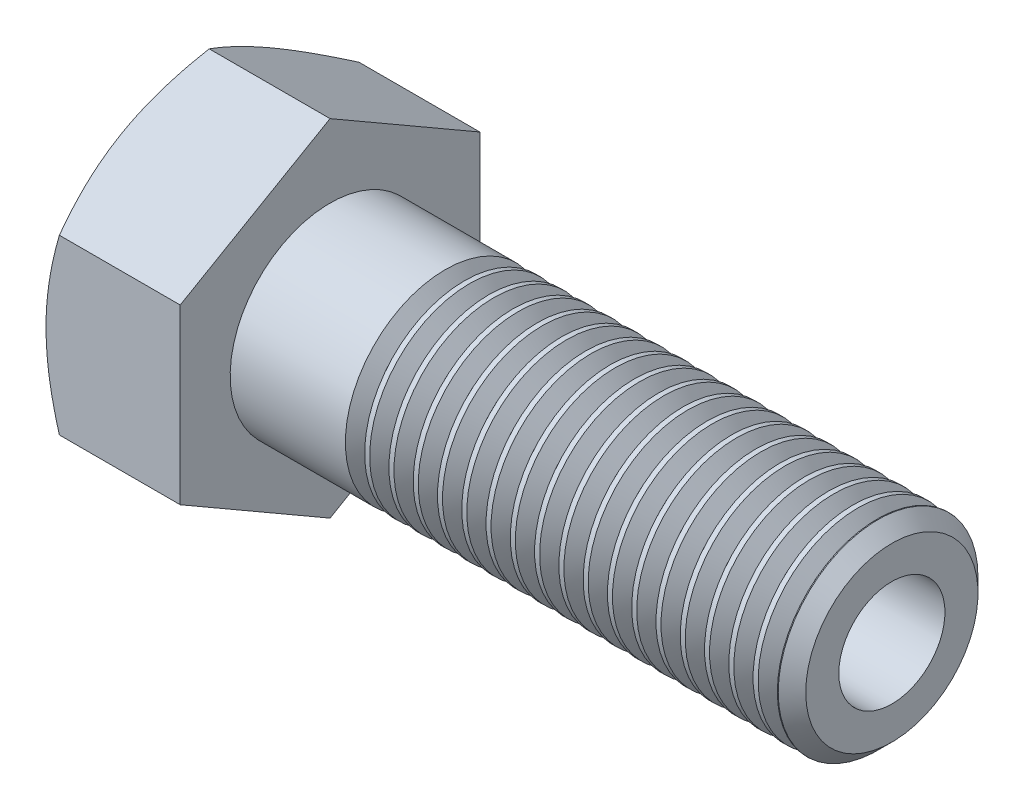
SolidWorks part; units mm, degrees
extrude "BaseHead" add sketch "Sketch1" along normal blind 10.75
sketch "Sketch1" plane through (0, 0, 0) normal (1, 0, 0) x (0, 0, -1)
  line L0 (12, 6.9282) -> (12, -6.9282)
  line L1 (-12, 6.9282) -> (-12, -6.9282)
  line L2 (12, -6.9282) -> (0, -13.8564)
  line L3 (0, -13.8564) -> (-12, -6.9282)
  line L4 (12, 6.9282) -> (0, 13.8564)
  line L5 (0, 13.8564) -> (-12, 6.9282)
  dimension "Width_flats" = 24
  dimension "D2" = 120
  dimension "D3" = 12
  dimension "D4" = 12
  dimension "D5" = 12
ref_plane "Plane1" through (0, 0, 0) normal (0, 0, 1) x (1, 0, 0)
ref_plane "Plane2" through (0, 0, 0) normal (0, 1, 0) x (1, 0, 0)
ref_plane "Plane3" through (0, 0, 0) normal (1, 0, 0) x (0, 0, -1)
sketch "BodySke" plane through (0, 0, 0) normal (0, 0, 1) x (1, 0, 0)
  line L0 (0, 6.9282) -> (0, -6.9282) construction
  line L1 (0, 0) -> (55.75, 0)
  line L2 (0, 0) -> (0, 8)
  line L3 (0, 8) -> (54.6485, 8)
  line L4 (55.75, 0) -> (55.75, 6.8985)
  line L5 (10.75, 13.8564) -> (10.75, 6.9282) construction
  line L6 (55.75, 6.8985) -> (54.6485, 8)
  line L7 (0, 0) -> (96.52, 0) construction
  line L8 (55.75, -6.8985) -> (54.6485, -8) construction
  line L9 (0, -8) -> (54.6485, -8) construction
  line L10 (12.75, 15.24) -> (12.75, -1.27) construction
  line L11 (20.75, 15.24) -> (20.75, -1.27) construction
  line L12 (10.75, 6.9282) -> (10.75, -6.9282) construction
  dimension "Diameter" = 16
revolve "BaseBody" add sketch "BodySke"
cosmetic thread "ThreadCosmetic" [suppressed]
fillet "HeadFillet" [suppressed] radius 0.6
sketch "Sketch3" plane through (0, 0, 0) normal (0, 0, 1) x (1, 0, 0)
  line L0 (0, 12) -> (3.9585, 18.8564)
  line L1 (0, 13.8564) -> (0, 6.9282) construction
  line L2 (3.9585, 18.8564) -> (3.9585, 23.8564)
  line L3 (3.9585, 23.8564) -> (-10, 23.8564)
  line L4 (-10, 23.8564) -> (-10, 12)
  line L5 (-10, 12) -> (0, 12)
  line L6 (0, 0) -> (99.06, 0) construction
  line L7 (10.75, 13.8564) -> (0, 13.8564) construction
  dimension "D1" = 12
  dimension "D2" = 5
  dimension "D3" = 10
  dimension "D4" = 5
  dimension "Head_ch_ang" = 30
revolve "HeadChamfer" cut sketch "Sketch3" angle 360 about L6
sketch "ThdSchSke" plane through (0, 0, 0) normal (0, 0, 1) x (1, 0, 0)
  line L0 (20.75, -6.8985) -> (19.9787, -8)
  line L1 (20.75, -6.8985) -> (21.5213, -8)
  line L2 (21.5213, -8) -> (21.5213, -10)
  line L3 (-3.175, 0) -> (5.1513, 0) construction
  line L5 (21.5213, -10) -> (19.9787, -10)
  line L6 (19.9787, -10) -> (19.9787, -8)
  dimension "Thread_minor" = 13.797
  dimension "Diameter" = 16
  dimension "Start" = 20.75
revolve "ThreadSchematic" cut sketch "ThdSchSke" angle 360 about L3
pattern_linear "ThdSchPat" count 18 spacing 1.9444 along (1, 0, 0) of "ThreadSchematic"
sketch "Sketch4" plane through (0, 0, 0) normal (-1, 0, 0) x (0, 0, 1)
  circle A0 centre (0, 0) radius 4.25
  dimension "D1" = 8.5
extrude "Cut-Extrude1" cut sketch "Sketch4" against normal through all
equation "\"D3@Sketch1\" = \"Width_flats@Sketch1\" / 2"
equation "\"D4@Sketch1\" = \"D3@Sketch1\""
equation "\"D5@Sketch1\" = \"D4@Sketch1\""
equation "\"Thread_minor@ThreadCosmetic\" = \"Minor_dia@BodySke\""
equation "\"D1@Sketch3\" = \"Width_flats@Sketch1\" / 2"
equation "' \"D1@Sketch4\" = \"Width_flats@Sketch1\""
equation "\"Thread_length@ThreadCosmetic\" = ((sgn( (\"Length@BodySke\" - \"Advance@BodySke\" ) - \"Thread_nom@BodySke\" )-1)*( (\"Length@BodySke\" - \"Advance@BodySke\" ) - \"Thread_nom@BodySke\" ))/-2+ \"Thread_nom@BodySke\""
equation "\"Thread_minor@ThdSchSke\" = \"Minor_dia@BodySke\""
equation "\"Diameter@ThdSchSke\" = \"Diameter@BodySke\""
equation "\"Overcut@ThdSchSke\" = \"Diameter@BodySke\" * 1.25"
equation "\"Start@ThdSchSke\" = \"Head_ht@BaseHead\" + \"Length@BodySke\" - \"Thread_length@ThreadCosmetic\"  '---Non-countersunk---"
equation "\"Num_threads@ThdSchPat\" = int( \"Thread_length@ThreadCosmetic\" / \"Advance@BodySke\" + 0.999 )  + 1"
equation "\"Advance@ThdSchPat\" = \"Thread_length@ThreadCosmetic\" /  (\"Num_threads@ThdSchPat\" - 1) 'relax it"
equation "\"Num_threads@ThdSchPat\" = \"Num_threads@ThdSchPat\" - sgn( \"Num_threads@ThdSchPat\" - 1) '---chamfered tips only---"
